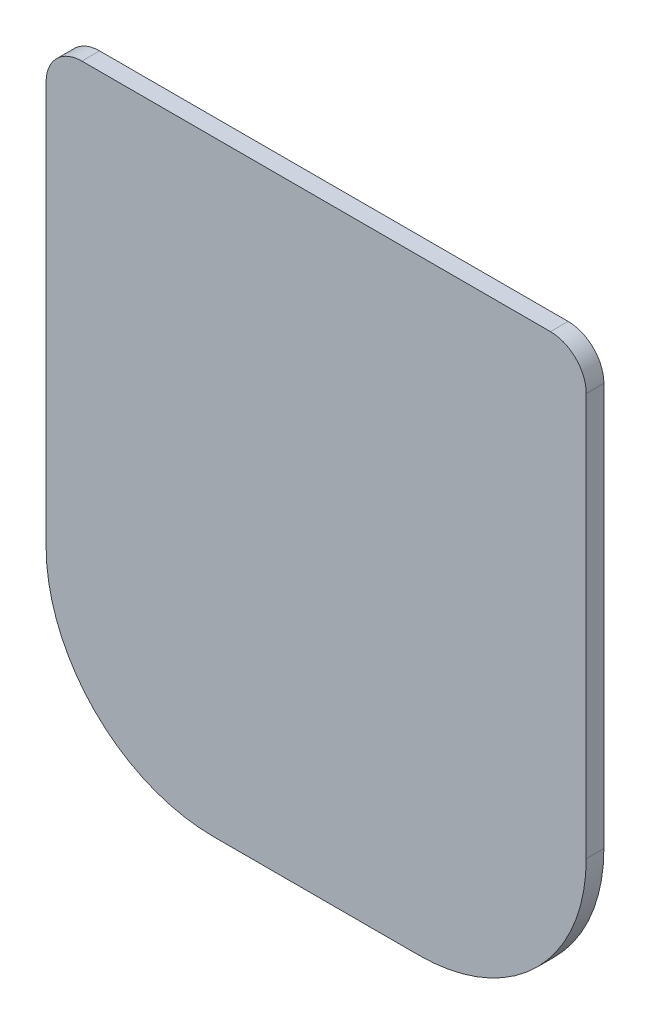
SolidWorks part; units mm, degrees
ref_plane "Front Plane" through (0, 0, 0) normal (0, 0, 1) x (1, 0, 0)
ref_plane "Top Plane" through (0, 0, 0) normal (0, 1, 0) x (1, 0, 0)
ref_plane "Right Plane" through (0, 0, 0) normal (1, 0, 0) x (0, 0, -1)
sketch "Sketch1" plane through (0, 0, 0) normal (0, 0, 1) x (1, 0, 0)
  line L0 (70, -39.19) -> (70, 58.81) construction
  line L1 (-25, -84.19) -> (-0.5, -84.19) construction
  line L2 (0.5, -84.19) -> (25, -84.19) construction
  line L3 (57, 71.81) -> (-57, 71.81) construction
  line L4 (70, 58.81) -> (-70, 58.81) construction
  line L5 (-70, 58.81) -> (-70, -39.19) construction
  line L6 (-0.5, -84.19) -> (0.5, -84.19) construction
  line L7 (-65.7, 58.81) -> (-65.7, -39.19)
  line L8 (-25, -79.89) -> (-0.5, -79.89)
  line L9 (-0.5, -79.89) -> (0.5, -79.89)
  line L10 (0.5, -79.89) -> (25, -79.89)
  line L11 (65.7, -39.19) -> (65.7, 58.81)
  line L12 (57, 67.51) -> (-57, 67.51)
  arc A0 (25, -84.19) -> (70, -39.19) centre (25, -39.19) ccw construction
  arc A1 (-70, -39.19) -> (-25, -84.19) centre (-25, -39.19) ccw construction
  arc A2 (70, 58.81) -> (57, 71.81) centre (57, 58.81) ccw construction
  arc A3 (-70, 58.81) -> (-57, 71.81) centre (-57, 58.81) cw construction
  arc A4 (-65.7, -39.19) -> (-25, -79.89) centre (-25, -39.19) ccw
  arc A5 (25, -79.89) -> (65.7, -39.19) centre (25, -39.19) ccw
  arc A6 (65.7, 58.81) -> (57, 67.51) centre (57, 58.81) ccw
  arc A7 (-65.7, 58.81) -> (-57, 67.51) centre (-57, 58.81) cw
  point P14 (0, 71.81)
  point P30 (0, 0)
  point P31 (0, 0)
  dimension "D1" = 13
  dimension "D2" = 98
  dimension "D3" = 4.3
  dimension "D4" = 156
  dimension "D5" = 71.81
  dimension "D6" = 140
extrude "Boss-Extrude1" add sketch "Sketch1" along normal blind 4.3
